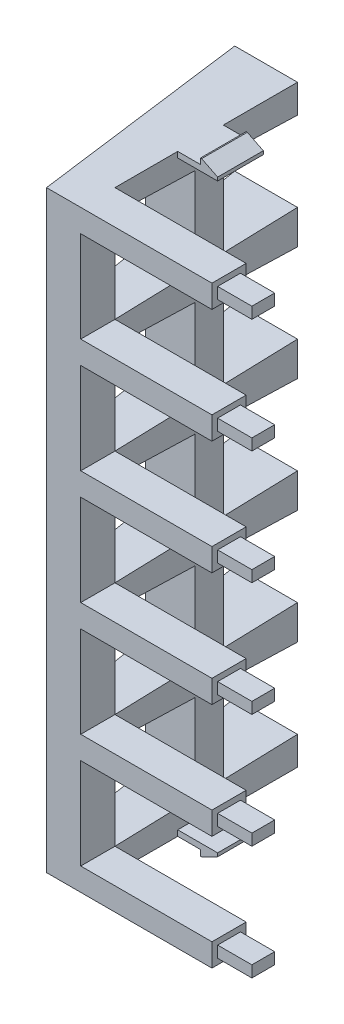
SolidWorks part; units mm, degrees
ref_plane "前视基准面" through (0, 0, 0) normal (0, 0, 1) x (1, 0, 0)
ref_plane "上视基准面" through (0, 0, 0) normal (0, 1, 0) x (1, 0, 0)
ref_plane "右视基准面" through (0, 0, 0) normal (1, 0, 0) x (0, 0, -1)
sketch "草图1" plane through (0, 0, 0) normal (0, 1, 0) x (1, 0, 0)
  line L0 (0, 19) -> (-2.5, 19)
  line L1 (0, 0) -> (17.5, 0)
  line L3 (0, 19) -> (3, 19)
  line L4 (17.5, 0) -> (17.5, 3)
  line L5 (3, 3) -> (17.5, 3)
  line L6 (3, 3) -> (3, 19)
  line L9 (-2.5, 19) -> (0, 0)
  dimension "D1" = 3
  dimension "D2" = 14.5
  dimension "D3" = 16
  dimension "D4" = 3
  dimension "D5" = 5.5
extrude "凸台-拉伸1" add sketch "草图1" along normal blind 52
sketch "草图2" plane through (0, 0, -3) normal (0, 0, -1) x (-1, 0, 0)
  line L0 (-17.5, 52) -> (-17.5, 0) construction
  line L1 (-17.5, 50) -> (-3, 50)
  line L2 (-17.5, 50) -> (-17.5, 42)
  line L3 (-17.5, 42) -> (-3, 42)
  line L4 (-3, 50) -> (-3, 42)
  line L5 (-3, 52) -> (-3, 0) construction
  line L6 (-17.5, 52) -> (-3, 52) construction
  dimension "D1" = 8
  dimension "D2" = 2
extrude "切除-拉伸1" cut sketch "草图2" against normal through all
pattern_linear "阵列(线性)1" count 5 spacing 10 along (0, -1, 0) of "切除-拉伸1"
sketch "草图4" plane through (3, 0, 0) normal (1, 0, 0) x (0, 0, -1)
  line L0 (3, 50) -> (3, 42)
  line L1 (3, 50) -> (10, 49.7812)
  line L2 (19, 49.5) -> (19, 42.5)
  line L3 (19, 42.5) -> (12.5, 42.2969)
  line L4 (3, 46) -> (25.3412, 46) construction
  line L5 (19, 52) -> (19, 0) construction
  line L6 (10, 49.7812) -> (10, 42.2188)
  line L7 (12.5, 49.7031) -> (12.5, 42.2969)
  line L8 (12.5, 49.7031) -> (19, 49.5)
  line L9 (10, 42.2188) -> (3, 42)
  dimension "D1" = 7
  dimension "D2" = 7
  dimension "D3" = 2.5
extrude "切除-拉伸2" cut sketch "草图4" against normal through all
pattern_linear "阵列(线性)2" count 5 spacing 10 along (0, -1, 0) of "切除-拉伸2"
sketch "草图5" plane through (17.5, 0, 0) normal (1, 0, 0) x (0, 0, -1)
  line L0 (0, 51) -> (3, 51) construction
  line L1 (0, 52) -> (0, 50) construction
  line L2 (3, 52) -> (3, 50) construction
  line L3 (1.5, 52) -> (1.5, 50) construction
  line L4 (0, 52) -> (3, 52) construction
  line L5 (0, 50) -> (3, 50) construction
  line L11 (0, 52) -> (3, 52)
  line L12 (0, 52) -> (0, 50)
  line L17 (0, 50) -> (3, 50)
  line L18 (3, 52) -> (3, 50)
  line L19 (2.5, 50.5) -> (0.5, 50.5)
  line L20 (2.5, 50.5) -> (2.5, 51.5)
  line L21 (2.5, 51.5) -> (0.5, 51.5)
  line L22 (0.5, 50.5) -> (0.5, 51.5)
  line L23 (2.5, 50.5) -> (0.5, 51.5) construction
  line L24 (2.5, 51.5) -> (0.5, 50.5) construction
  point P12 (1.5, 51)
  point P17 (1.5, 51)
  point P18 (1.5, 51)
  dimension "D1" = 2
  dimension "D2" = 1
extrude "切除-拉伸3" cut sketch "草图5" against normal blind 3
pattern_linear "阵列(线性)3" count 6 spacing 10 along (0, -1, 0) of "切除-拉伸3"
sketch "草图6" plane through (3, 0, 0) normal (1, 0, 0) x (0, 0, -1)
  line L0 (3, 0) -> (19, 0) construction
  line L2 (8.5, 0) -> (8.5, 0.5)
  line L3 (8.5, 0.5) -> (12.5, 0.5)
  line L4 (12.5, 0) -> (12.5, 0.5)
  line L5 (3, 10) -> (3, 2) construction
  line L8 (8.5, 0) -> (8.5, -0.5)
  line L9 (8.5, -0.5) -> (12.5, -0.5)
  line L10 (12.5, 0) -> (12.5, -0.5)
  dimension "D1" = 5.5
  dimension "D2" = 4
  dimension "D3" = 0.5
  dimension "D4" = 0.5
extrude "凸台-拉伸2" add sketch "草图6" along normal blind 3.5
sketch "草图8" plane through (0, 0, -8.5) normal (0, 0, 1) x (1, 0, 0)
  line L0 (3, 0) -> (3, -0.5)
  line L1 (3, -0.5) -> (5, -0.5)
  line L2 (6.5, -0.5) -> (3, -0.5) construction
  line L3 (5, -0.5) -> (5, 0)
  line L4 (0, 0) -> (14.5, 0) construction
  line L5 (5, 0) -> (3, 0)
  line L6 (6.5, -0.5) -> (5.1, -0.5)
  line L7 (5.1, -0.5) -> (6.5, 0.2)
  line L8 (6.5, 0.5) -> (6.5, -0.5) construction
  line L9 (6.5, 0.5) -> (3, 0.5) construction
  line L10 (6.5, 0.2) -> (6.5, -0.5)
  dimension "D1" = 0.3
  dimension "D2" = 0.1
  dimension "D3" = 1.5
extrude "切除-拉伸4" cut sketch "草图8" against normal blind 5
ref_plane "基准面1" through (0, 26, 0) normal (0, 1, 0) x (1, 0, 0)
mirror "镜向1" about plane through (0, 26, 0) normal (0, 1, 0) of "凸台-拉伸2", "切除-拉伸4"
